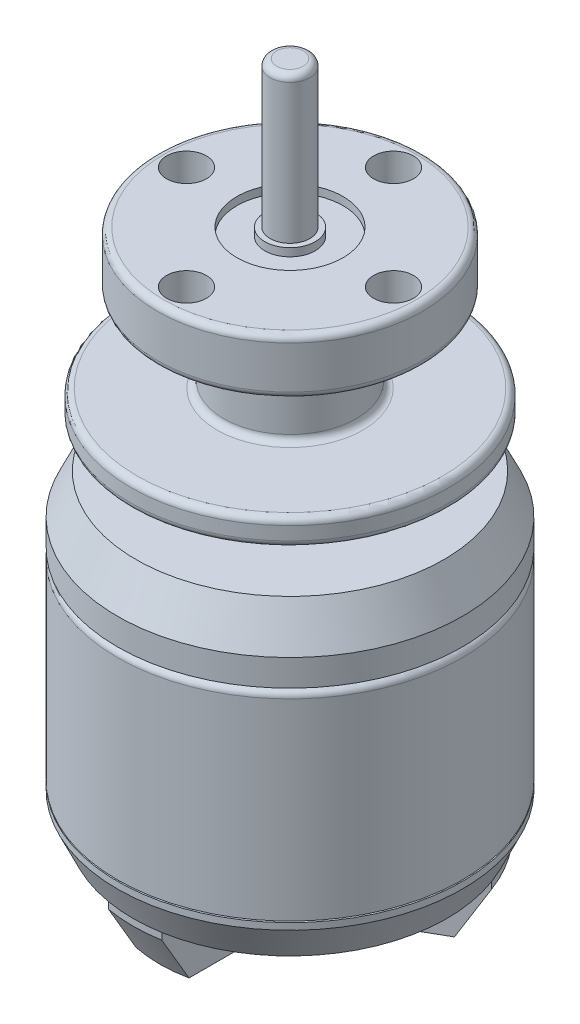
SolidWorks part; units mm, degrees
ref_plane "Front Plane" through (0, 0, 0) normal (0, 0, 1) x (1, 0, 0)
ref_plane "Top Plane" through (0, 0, 0) normal (0, 1, 0) x (1, 0, 0)
ref_plane "Right Plane" through (0, 0, 0) normal (1, 0, 0) x (0, 0, -1)
sketch "Sketch1" plane through (0, 0, 0) normal (0, 1, 0) x (1, 0, 0)
  circle A0 centre (0, 0) radius 13
  dimension "D1" = 26
extrude "Boss-Extrude1" add sketch "Sketch1" along normal blind 15
sketch "Sketch2" plane through (0, 15, 0) normal (0, 1, 0) x (1, 0, 0)
  circle A0 centre (0, 0) radius 7
extrude "Boss-Extrude2" add sketch "Sketch2" along normal blind 0.2
sketch "Sketch4" plane through (0, 15.2, 0) normal (0, 1, 0) x (1, 0, 0)
  circle A0 centre (0, 0) radius 13
extrude "Boss-Extrude3" add sketch "Sketch4" along normal blind 5
sketch "Sketch5" plane through (0, 20.2, 0) normal (0, 1, 0) x (1, 0, 0)
  circle A0 centre (0, 0) radius 5
extrude "Boss-Extrude4" add sketch "Sketch5" along normal blind 3.4
sketch "Sketch6" plane through (0, 23.6, 0) normal (0, 1, 0) x (1, 0, 0)
  circle A0 centre (0, 0) radius 12
extrude "Boss-Extrude5" add sketch "Sketch6" along normal blind 2
sketch "Sketch7" plane through (0, 25.6, 0) normal (0, 1, 0) x (1, 0, 0)
  circle A0 centre (0, 0) radius 5
extrude "Boss-Extrude6" add sketch "Sketch7" along normal blind 6.3
sketch "Sketch8" plane through (0, 31.9, 0) normal (0, 1, 0) x (1, 0, 0)
  circle A0 centre (0, 0) radius 10
extrude "Boss-Extrude7" add sketch "Sketch8" along normal blind 4.2
chamfer "Chamfer1" distance 3 angle 25 1 edges at (0, 20.2, 13)
fillet "Fillet1" radius 0.5 9 edges at (0, 31.9, 10) (0, 36.1, 10) (0, 23.6, 12) (0, 25.6, 12) (0, 15, 13) (0, 20.2, 5) (0, 23.6, 5) (0, 25.6, 5) (0, 31.9, 5)
sketch "Sketch9" plane through (0, 0, 0) normal (0, -1, 0) x (1, 0, 0)
  circle A0 centre (0, 0) radius 8.4636
extrude "Boss-Extrude8" add sketch "Sketch9" along normal blind 0.1
sketch "Sketch10" plane through (0, -0.1, 0) normal (0, -1, 0) x (1, 0, 0)
  circle A0 centre (0, 0) radius 13
extrude "Boss-Extrude9" add sketch "Sketch10" along normal blind 3
chamfer "Chamfer2" distance 2.5 angle 25 1 edges at (0, -3.1, -13)
sketch "Sketch12" plane through (0, -3.1, 0) normal (0, -1, 0) x (1, 0, 0)
  line L0 (0, 11.8342) -> (0, 0) construction
  line L1 (0, 0) -> (10.2487, -5.9171) construction
  line L2 (0, 0) -> (-10.2487, -5.9171) construction
  line L3 (-11.2487, -4.1851) -> (-1, 1.7321)
  line L4 (-11.2487, -4.1851) -> (-9.2487, -7.6492)
  line L5 (-1, 1.7321) -> (1, -1.7321)
  line L6 (-9.2487, -7.6492) -> (1, -1.7321)
  line L7 (-11.2487, -4.1851) -> (1, -1.7321) construction
  line L8 (-1, 1.7321) -> (-9.2487, -7.6492) construction
  line L9 (-2, 0) -> (-2, 11.8342)
  line L10 (-2, 0) -> (2, 0)
  line L11 (-2, 11.8342) -> (2, 11.8342)
  line L12 (2, 0) -> (2, 11.8342)
  line L13 (-2, 0) -> (2, 11.8342) construction
  line L14 (-2, 11.8342) -> (2, 0) construction
  line L15 (1, 1.7321) -> (11.2487, -4.1851)
  line L16 (1, 1.7321) -> (-1, -1.7321)
  line L17 (11.2487, -4.1851) -> (9.2487, -7.6492)
  line L18 (-1, -1.7321) -> (9.2487, -7.6492)
  line L19 (1, 1.7321) -> (9.2487, -7.6492) construction
  line L20 (11.2487, -4.1851) -> (-1, -1.7321) construction
  circle A0 centre (0, 0) radius 5
  circle A1 centre (0, 0) radius 11.8342 construction
  circle A2 centre (0, 0) radius 11.8342
  point P9 (-5.1244, -2.9586)
  point P10 (0, 5.9171)
  point P15 (5.1244, -2.9586)
  circle M10 centre (0, 0) radius 11.8342
extrude "Boss-Extrude10" add sketch "Sketch12" along normal blind 4 contours A0 L3 L6 M10 | L3 A0 L6 L18 L16 L10 L9 | L6 A0 L18 | L18 A0 L15 L12 L10 L5 L6 | A0 L18 L15 M10 | L16 L18 L6 L5 | L15 L16 L10 L12 | L15 A0 L12 | L12 A0 L9 L3 L5 L16 L15 | L9 A0 L3 | A0 L12 L9 M10 | L9 L10 L5 L3
chamfer "Chamfer3" distance 3.5 angle 30 3 edges at (0, -7.1, 11.8342) (10.2487, -7.1, -5.9171) (-10.2487, -7.1, -5.9171)
sketch "Sketch13" plane through (0, -3.1, 0) normal (0, -1, 0) x (1, 0, 0)
  circle A0 centre (0, 0) radius 10.7706
extrude "Cut-Extrude1" cut sketch "Sketch13" against normal blind 4
sketch "Sketch14" plane through (0, -7.1, 0) normal (0, -1, 0) x (1, 0, 0)
  circle A0 centre (0, 0) radius 4.5
extrude "Boss-Extrude11" add sketch "Sketch14" along normal blind 1
fillet "Fillet2" radius 0.7 1 edges at (0, -8.1, -4.5)
fillet "Fillet3" radius 2 6 edges at (-2, -5.1, 4.5826) (-4.9686, -5.1, -0.5592) (2, -5.1, 4.5826) (4.9686, -5.1, -0.5592) (2.9686, -5.1, -4.0233) (-2.9686, -5.1, -4.0233)
sketch "Sketch15" plane through (0, -7.1, 0) normal (0, -1, 0) x (1, 0, 0)
  circle A0 centre (0, 6.5) radius 1.5
  dimension "D1" = 6.5
  dimension "D2" = 3
extrude "Cut-Extrude2" cut sketch "Sketch15" against normal blind 4
pattern_circular "CirPattern1" count 3 over 360 about axis through (0, 0, 0) along (0, 1, 0) of "Cut-Extrude2"
sketch "Sketch16" plane through (0, -8.1, 0) normal (0, -1, 0) x (1, 0, 0)
  circle A0 centre (0, 0) radius 1.5
  circle A1 centre (0, 0) radius 1.7
extrude "Cut-Extrude3" cut sketch "Sketch16" against normal blind 2
fillet "Fillet4" radius 0.3 1 edges at (0, -8.1, -1.5)
sketch "Sketch17" plane through (0, 36.1, 0) normal (0, 1, 0) x (1, 0, 0)
  circle A0 centre (0, 0) radius 4
  circle A1 centre (0, 0) radius 1.9
extrude "Cut-Extrude4" cut sketch "Sketch17" against normal blind 0.6
sketch "Sketch18" plane through (0, 36.1, 0) normal (0, 1, 0) x (1, 0, 0)
  circle A1 centre (0, 0) radius 1.5
extrude "Boss-Extrude12" add sketch "Sketch18" along normal blind 11
fillet "Fillet5" radius 0.5 1 edges at (0, 47.1, 1.5)
sketch "Sketch19" plane through (0, 36.1, 0) normal (0, 1, 0) x (1, 0, 0)
  circle A0 centre (0, 7.8) radius 1.5
  dimension "D1" = 3
  dimension "D2" = 7.8
extrude "Cut-Extrude5" cut sketch "Sketch19" against normal blind 5
pattern_circular "CirPattern2" count 4 over 360 about axis through (0, 0, 0) along (0, 1, 0) of "Cut-Extrude5"
